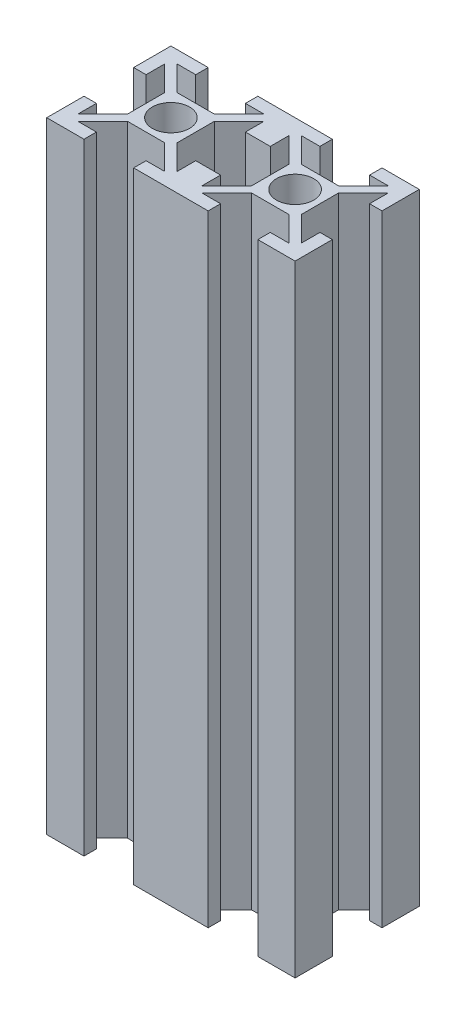
SolidWorks part; units mm, degrees
material "1060 Alloy"
ref_plane "Front Plane" through (0, 0, 0) normal (0, 0, 1) x (1, 0, 0)
ref_plane "Top Plane" through (0, 0, 0) normal (0, 1, 0) x (1, 0, 0)
ref_plane "Right Plane" through (0, 0, 0) normal (1, 0, 0) x (0, 0, -1)
sketch "2020 sketch" plane through (0, 0, 0) normal (0, 1, 0) x (1, 0, 0)
  line L0 (-4, 10) -> (-4, 8)
  line L1 (-10, 10) -> (-4, 10)
  line L2 (-10, 10) -> (-10, 4)
  line L3 (-10, -10) -> (-4, -10)
  line L4 (10, 10) -> (10, 4)
  line L5 (-10, 10) -> (10, -10) construction
  line L6 (-10, -10) -> (10, 10) construction
  line L7 (-4, 8) -> (-7, 8)
  line L8 (-7, 8) -> (-3, 4)
  line L9 (-3, 4) -> (3, 4)
  line L10 (3, 4) -> (7, 8)
  line L11 (7, 8) -> (4, 8)
  line L12 (4, 8) -> (4, 10)
  line L13 (4, 3) -> (4, -3)
  line L14 (8, 7) -> (4, 3)
  line L15 (8, 4) -> (8, 7)
  line L16 (10, 4) -> (8, 4)
  line L17 (8, -4) -> (10, -4)
  line L18 (8, -7) -> (8, -4)
  line L19 (4, -3) -> (8, -7)
  line L20 (3, -4) -> (-3, -4)
  line L21 (7, -8) -> (3, -4)
  line L22 (4, -8) -> (7, -8)
  line L23 (4, -10) -> (4, -8)
  line L24 (-4, -8) -> (-4, -10)
  line L25 (-7, -8) -> (-4, -8)
  line L26 (-3, -4) -> (-7, -8)
  line L27 (-4, -3) -> (-4, 3)
  line L28 (-8, -7) -> (-4, -3)
  line L29 (-8, -4) -> (-8, -7)
  line L30 (-10, -4) -> (-8, -4)
  line L31 (-8, 4) -> (-10, 4)
  line L32 (-8, 7) -> (-8, 4)
  line L33 (-4, 3) -> (-8, 7)
  line L34 (-10, -4) -> (-10, -10)
  line L35 (10, -4) -> (10, -10)
  line L36 (4, 10) -> (10, 10)
  line L37 (4, -10) -> (10, -10)
  circle A0 centre (0, 0) radius 3
  point P0 (0, 0)
  point P14 (4, 9)
  point P42 (0, 0)
  dimension "D9" = 6
  dimension "D1" = 20
  dimension "D2" = 20
  dimension "D3" = 8
  dimension "D4" = 6
  dimension "D5" = 6
  dimension "D6" = 2
  dimension "D7" = 4
  dimension "D8" = 4
extrude "Boss-Extrude1" add sketch "2020 sketch" along normal blind 100 contours A0 | L28 L27 L33 L32 L31 L2 L1 L0 L7 L8 L9 L10 L11 L12 L36 L4 L16 L15 L14 L13 L19 L18 L17 L35 L37 L23 L22 L21 L20 L26 L25 L24 L3 L34 L30 L29
mirror "Mirror1" about plane through (10, 100, 4) normal (1, 0, 0) of "Boss-Extrude1"
